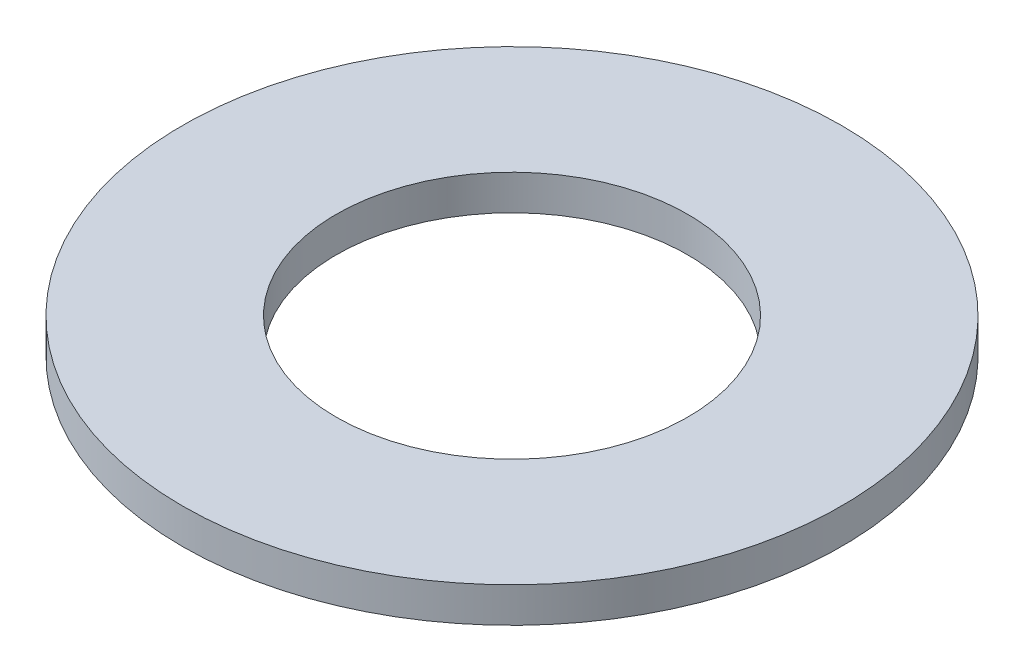
SolidWorks part; units mm, degrees
ref_plane "Front Plane" through (0, 0, 0) normal (0, 0, 1) x (1, 0, 0)
ref_plane "Top Plane" through (0, 0, 0) normal (0, 1, 0) x (1, 0, 0)
ref_plane "Right Plane" through (0, 0, 0) normal (1, 0, 0) x (0, 0, -1)
sketch "Sketch1" plane through (0, 0, 0) normal (0, 1, 0) x (1, 0, 0)
  circle A0 centre (0, 0) radius 4
  circle A1 centre (0, 0) radius 7.5
  dimension "D1" = 8
  dimension "D2" = 15
extrude "Boss-Extrude1" add sketch "Sketch1" along normal blind 0.8
